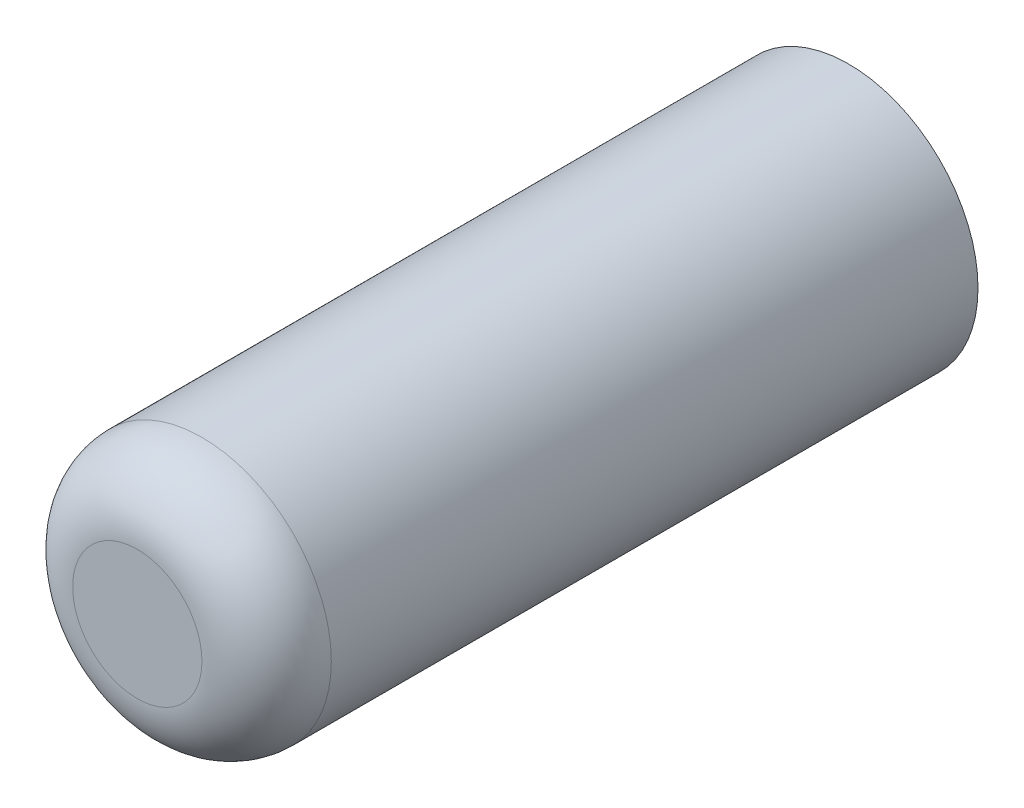
SolidWorks part; units mm, degrees
material "Messing"
ref_plane "Ebene vorne" through (0, 0, 0) normal (0, 0, 1) x (1, 0, 0)
ref_plane "Ebene oben" through (0, 0, 0) normal (0, 1, 0) x (1, 0, 0)
ref_plane "Ebene rechts" through (0, 0, 0) normal (1, 0, 0) x (0, 0, -1)
sketch "Skizze1" plane through (0, 0, 0) normal (0, 0, 1) x (1, 0, 0)
  circle A0 centre (0, 0) radius 4
  dimension "D1" = 8
extrude "Aufsatz-Linear austragen1" add sketch "Skizze1" along normal blind 22
cosmetic thread "Gewindedarstellung1" parameters "D1"=17, "D2"=6.619
fillet "Verrundung1" radius 2 1 edges at (4, 0, 22)
